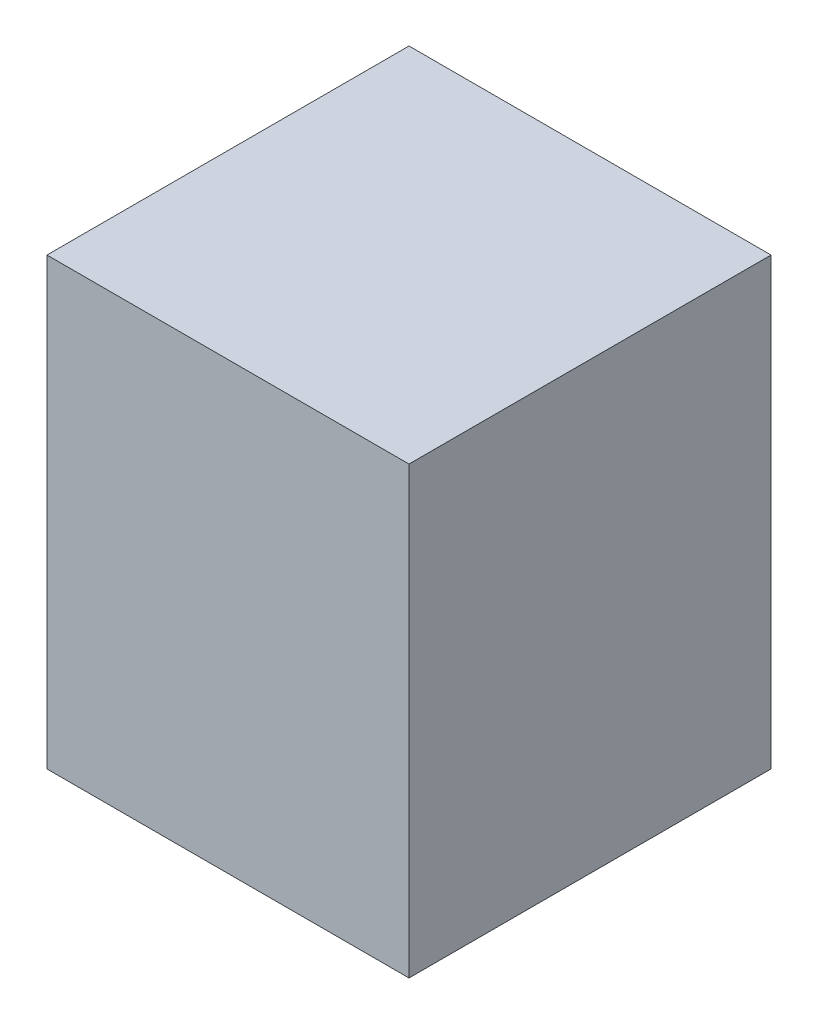
SolidWorks part; units mm, degrees
ref_plane "Front" through (0, 0, 0) normal (0, 0, 1) x (1, 0, 0)
ref_plane "Top" through (0, 0, 0) normal (0, 1, 0) x (1, 0, 0)
ref_plane "Right" through (0, 0, 0) normal (1, 0, 0) x (0, 0, -1)
sketch "Sketch3" plane through (0, 0, 0) normal (0, 1, 0) x (1, 0, 0)
  line L1 (-193.675, -193.675) -> (193.675, -193.675)
  line L2 (-193.675, -193.675) -> (-193.675, 193.675)
  line L3 (-193.675, 193.675) -> (193.675, 193.675)
  line L4 (193.675, -193.675) -> (193.675, 193.675)
  line L5 (-193.675, -193.675) -> (193.675, 193.675) construction
  line L6 (-193.675, 193.675) -> (193.675, -193.675) construction
  point P0 (0, 0)
  dimension "D1" = 387.35
extrude "Boss-Extrude1" add sketch "Sketch3" along normal mid plane 476.25
sketch "Sketch6" plane through (0, 0, 0) normal (1, 0, 0) x (0, 0, -1)
  line L0 (193.675, 241.125) -> (193.675, 238.125) construction
  line L1 (-193.675, -238.125) -> (193.675, -238.125)
  line L2 (-193.675, -238.125) -> (-193.675, 238.125)
  line L3 (-193.675, 238.125) -> (193.675, 238.125)
  line L4 (193.675, -238.125) -> (193.675, 238.125)
  line L5 (-193.675, -238.125) -> (193.675, 238.125) construction
  line L6 (-193.675, 238.125) -> (193.675, -238.125) construction
  line L7 (-196.675, -241.125) -> (196.675, -241.125)
  line L8 (-196.675, -241.125) -> (-196.675, 241.125)
  line L9 (-196.675, 241.125) -> (196.675, 241.125)
  line L10 (196.675, -241.125) -> (196.675, 241.125)
  line L11 (-196.675, -241.125) -> (196.675, 241.125) construction
  line L12 (-196.675, 241.125) -> (196.675, -241.125) construction
  line L13 (193.675, 238.125) -> (196.675, 238.125) construction
  line L14 (0, 0) -> (-193.675, 0) construction
  point P0 (0, 0)
  point P7 (0, 0)
  dimension "D1" = 3
equation "\"acrylic_thickness\"=3"
